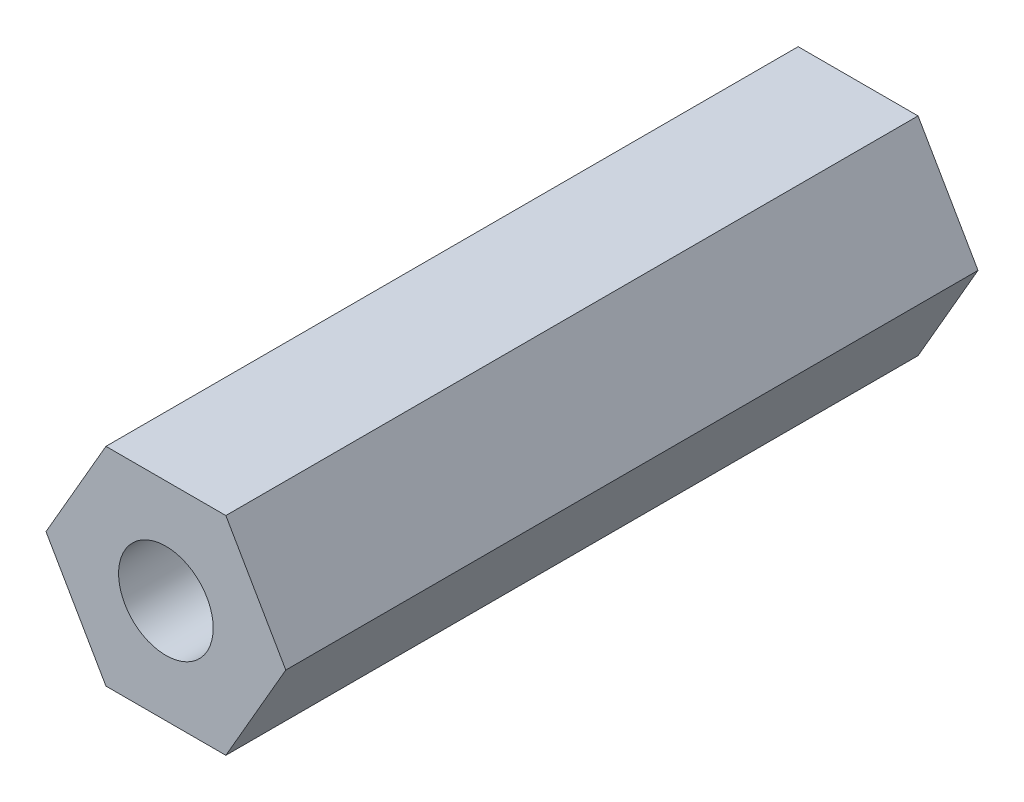
SolidWorks part; units mm, degrees
material "Delrin 2700 NC010, Low Viscosity Acetal Copolymer (SS)"
ref_plane "Front Plane" through (0, 0, 0) normal (0, 0, 1) x (1, 0, 0)
ref_plane "Top Plane" through (0, 0, 0) normal (0, 1, 0) x (1, 0, 0)
ref_plane "Right Plane" through (0, 0, 0) normal (1, 0, 0) x (0, 0, -1)
sketch "Sketch1" plane through (0, 0, 0) normal (0, 0, 1) x (1, 0, 0)
  line L1 (-1.299, 2.25) -> (-2.5981, 0)
  line L2 (-2.5981, 0) -> (-1.299, -2.25)
  line L3 (-1.299, -2.25) -> (1.299, -2.25)
  line L4 (1.299, -2.25) -> (2.5981, 0)
  line L5 (2.5981, 0) -> (1.299, 2.25)
  line L6 (1.299, 2.25) -> (-1.299, 2.25)
  circle A0 centre (0, 0) radius 2.25 construction
  dimension "D1" = 4.5
extrude "Boss-Extrude1" add sketch "Sketch1" along normal blind 15
hole_wizard "Tap Drill for M2.5 Tap1" positions "Sketch3" profile "Sketch2" hole size "M2.5" standard "DIN"
sketch "Sketch3" plane through (0, 0, 15) normal (0, 0, 1) x (1, 0, 0)
  point P0 (0, 0)
sketch "Sketch2" plane through (0, 0, 15) normal (1, 0, 0) x (0, -1, 0)
  line L0 (0, 0) -> (0, 11.5)
  line L1 (0, 11.5) -> (1.025, 11.5)
  line L2 (1.025, 11.5) -> (1.025, 0)
  line L5 (1.025, 0) -> (0, 0)
  line L10 (0, 11.5) -> (-1.025, 11.5) construction
  line L11 (0, -6.35) -> (0, 107.95) construction
  dimension "Hole Dia." = 2.05
  dimension "Hole Depth" = 11.5
  dimension "Drill Angle" = 180
